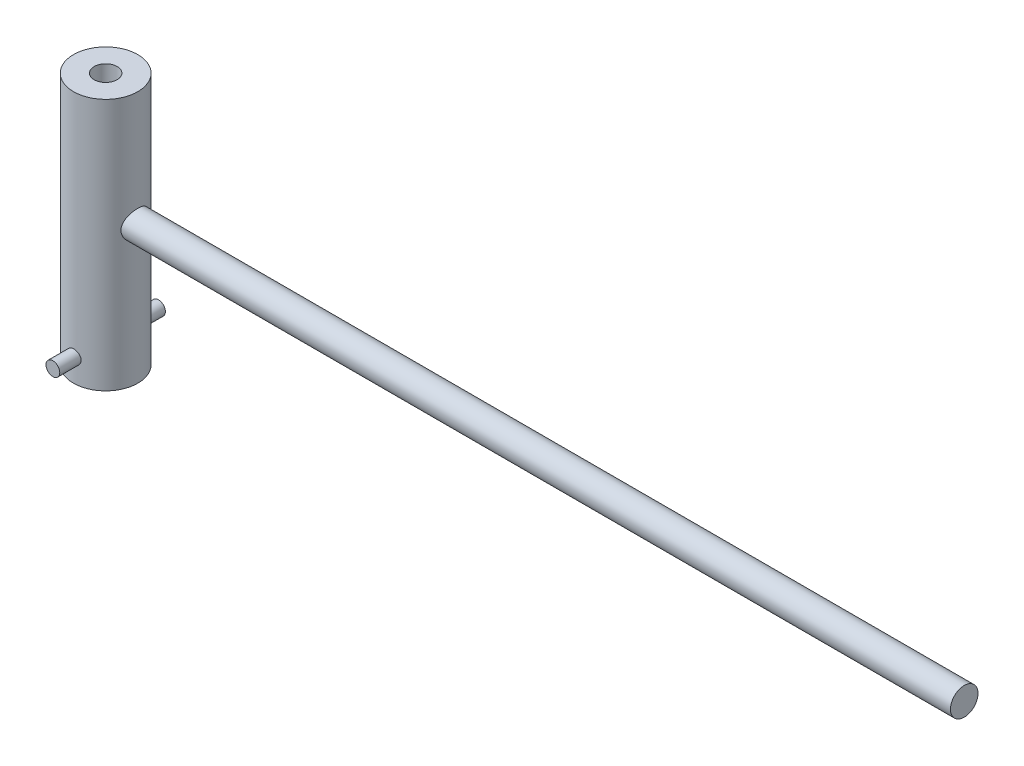
SolidWorks part; units mm, degrees
ref_plane "Plan de face" through (0, 0, 0) normal (0, 0, 1) x (1, 0, 0)
ref_plane "Plan de dessus" through (0, 0, 0) normal (0, 1, 0) x (1, 0, 0)
ref_plane "Plan de droite" through (0, 0, 0) normal (1, 0, 0) x (0, 0, -1)
sketch "Esquisse1" plane through (0, 0, 0) normal (0, 0, 1) x (1, 0, 0)
  line L0 (0, 0) -> (0, -60.0519) construction
  line L1 (0, 0) -> (7, 0)
  line L2 (7, 0) -> (7, -55)
  line L3 (7, -55) -> (0, -55)
  line L4 (0, 0) -> (0, -55)
  dimension "D1" = 55
  dimension "D2" = 7
revolve "Révolution1" add sketch "Esquisse1" angle 360 about L0
sketch "Esquisse2" plane through (0, 0, 0) normal (0, 0, 1) x (1, 0, 0)
  line L0 (-18.3587, -25) -> (18.2432, -25) construction
  line L1 (-7, -55) -> (7, -55) construction
  line L2 (7, -25) -> (7, -22)
  line L3 (7, -55) -> (7, 0) construction
  line L4 (7, -22) -> (77, -22)
  line L5 (77, -22) -> (77, -25)
  line L6 (7, -25) -> (77, -25)
  dimension "D1" = 30
  dimension "D2" = 3
  dimension "D3" = 70
revolve "Révolution2" add sketch "Esquisse2" angle 360 about L0
sketch "Esquisse3" plane through (0, 0, 0) normal (1, 0, 0) x (0, 0, -1)
  line L0 (-15.1196, -50) -> (17.7875, -50) construction
  line L1 (-7, -50) -> (-7, -48.5)
  line L2 (-7, -50) -> (-9, -50)
  line L3 (-7, 0) -> (-7, -55) construction
  line L4 (-7, -48.5) -> (-9, -48.5)
  line L5 (-9, -48.5) -> (-9, -50)
  line L6 (-7, -55) -> (7, -55) construction
  dimension "D1" = 1.5
  dimension "D2" = 2
  dimension "D3" = 5
revolve "Révolution4" add sketch "Esquisse3" angle 360 about L0
sketch "Esquisse4" plane through (0, 0, 0) normal (1, 0, 0) x (0, 0, -1)
  line L0 (-17.9731, -50) -> (18.6377, -50) construction
  line L1 (6.967, -50) -> (7, -48.5)
  line L2 (7, -55) -> (7, 0) construction
  line L3 (7, -48.5) -> (9, -48.5)
  line L4 (9, -48.5) -> (9, -50)
  line L5 (-7, -55) -> (7, -55) construction
  line L6 (6.967, -50) -> (9, -50)
  dimension "D1" = 2
  dimension "D2" = 1.5
  dimension "D3" = 5
revolve "Révolution5" add sketch "Esquisse4" angle 360 about L0
sketch "Esquisse5" plane through (0, 0, 0) normal (0, 1, 0) x (1, 0, 0)
  circle A0 centre (0, 0) radius 2.5
  dimension "D1" = 5
extrude "Enlèv. mat.-Extru.1" cut sketch "Esquisse5" against normal through all
sketch "Esquisse6" plane through (0, 0, 9) normal (0, 0, 1) x (1, 0, 0)
  circle A0 centre (0, -50) radius 1.5
  circle A1 centre (0, -50) radius 1.5 construction
sketch "Esquisse7" plane through (0, 0, 9) normal (0, 0, 1) x (1, 0, 0)
  circle A0 centre (0, -50) radius 1.4932
sketch "Esquisse8" plane through (0, 0, 9) normal (0, 0, 1) x (1, 0, 0)
  circle A0 centre (0, -50) radius 1.5
  dimension "D1" = 3
extrude "Boss.-Extru.1" add sketch "Esquisse8" along normal blind 2.5 and the other way blind 3
sketch "Esquisse11" plane through (0, 0, -9) normal (0, 0, -1) x (-1, 0, 0)
  circle A0 centre (0, -50) radius 1.5
  circle A1 centre (0, -50) radius 1.5 construction
  dimension "D1" = 3
extrude "Boss.-Extru.2" add sketch "Esquisse11" along normal blind 2.5 and the other way blind 3
sketch "Esquisse12" plane through (77, 0, 0) normal (1, 0, 0) x (0, 0, -1)
  circle A0 centre (0, -25) radius 3
  dimension "D1" = 6
extrude "Boss.-Extru.3" add sketch "Esquisse12" against normal blind 71.5 and the other way blind 110
